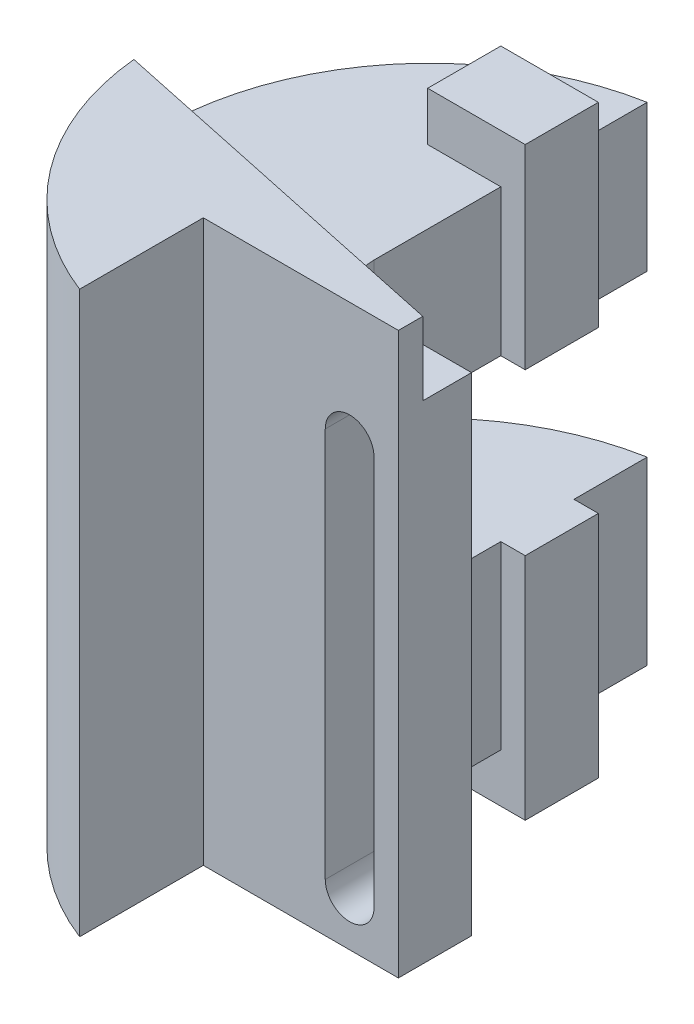
SolidWorks part; units mm, degrees
material "1060 Alloy"
ref_plane "Front Plane" through (0, 0, 0) normal (0, 0, 1) x (1, 0, 0)
ref_plane "Top Plane" through (0, 0, 0) normal (0, 1, 0) x (1, 0, 0)
ref_plane "Right Plane" through (0, 0, 0) normal (1, 0, 0) x (0, 0, -1)
sketch "Sketch1" plane through (0, 0, 0) normal (0, 1, 0) x (1, 0, 0)
  line L0 (0, 0) -> (0, 15)
  line L1 (0, 0) -> (-40, 0)
  line L2 (-40, 0) -> (-40, -25.3628)
  line L3 (0, 15) -> (-20, 15)
  line L4 (-30, 25) -> (-30, 81)
  arc A0 (-20, 15) -> (-30, 25) centre (-20, 25) cw
  arc A1 (-30, 81) -> (-40, -25.3628) centre (-20, 26.4083) ccw
  dimension "D3" = 10
  dimension "D7" = 55.5
  dimension "D1" = 15
  dimension "D2" = 40
  dimension "D4" = 30
  dimension "D5" = 66
  dimension "D6" = 10
extrude "Boss-Extrude1" add sketch "Sketch1" along normal blind 100
sketch "Sketch2" plane through (0, 100, 0) normal (0, 1, 0) x (1, 0, 0)
  line L0 (0, 5) -> (-75.235, 20.9917)
  line L1 (0, 0) -> (0, 15) construction
  line L2 (-40, 0) -> (0, 0) construction
  line L3 (-40, -25.3628) -> (-40, 0) construction
  line L4 (0, 0) -> (0, 5)
  line L5 (-40, 0) -> (0, 0)
  line L6 (-40, -25.3628) -> (-40, 0)
  arc A0 (-30, 81) -> (-40, -25.3628) centre (-20, 26.4083) ccw construction
  arc A1 (-75.235, 20.9917) -> (-40, -25.3628) centre (-20, 26.4083) ccw
  dimension "D1" = 5
  dimension "D2" = 78
extrude "Boss-Extrude2" add sketch "Sketch2" along normal blind 15
ref_plane "Plane1" through (0, 50, 0) normal (0, 1, 0) x (1, 0, 0)
sketch "Sketch3" plane through (0, 50, 0) normal (0, 1, 0) x (1, 0, 0)
  line L0 (-30, 25) -> (-30, 81) construction
  line L1 (-25, 66) -> (-45, 66)
  line L2 (-25, 66) -> (-25, 51)
  line L3 (-25, 51) -> (-45, 51)
  line L4 (-45, 66) -> (-45, 51)
  point P6 (0, 0)
  dimension "D1" = 5
  dimension "D2" = 15
  dimension "D3" = 15
  dimension "D4" = 20
extrude "Boss-Extrude3" add sketch "Sketch3" along normal mid plane 120
sketch "Sketch4" plane through (0, 0, 0) normal (1, 0, 0) x (0, 0, -1)
  line L0 (81, 100) -> (81, 0) construction
  line L1 (81, 70) -> (41, 70)
  line L2 (81, 70) -> (81, 37)
  line L3 (81, 37) -> (41, 37)
  line L4 (41, 70) -> (41, 37)
  line L5 (66, 100) -> (81, 100) construction
  line L6 (51, 110) -> (51, -10) construction
  dimension "D1" = 30
  dimension "D2" = 33
  dimension "D3" = 10
extrude "Cut-Extrude1" cut sketch "Sketch4" against normal mid plane 239
sketch "Sketch5" plane through (0, 0, -15) normal (0, 0, -1) x (-1, 0, 0)
  line L0 (10, 90) -> (10, 10) construction
  line L1 (15, 90) -> (15, 10)
  line L2 (5, 90) -> (5, 10)
  line L3 (0, 100) -> (75.235, 100) construction
  line L4 (0, 0) -> (20, 0) construction
  line L5 (0, 115) -> (0, 100) construction
  arc A0 (15, 90) -> (5, 90) centre (10, 90) ccw
  arc A1 (5, 10) -> (15, 10) centre (10, 10) ccw
  point P2 (10, 50)
  point P11 (0, 0)
  dimension "D3" = 5
  dimension "D1" = 10
  dimension "D2" = 10
  dimension "D4" = 10
extrude "Cut-Extrude2" cut sketch "Sketch5" against normal mid plane 239
equation "\"a\"= 55.5mm"
equation "\"b\"= 66mm"
equation "\"c\"= 33mm"
